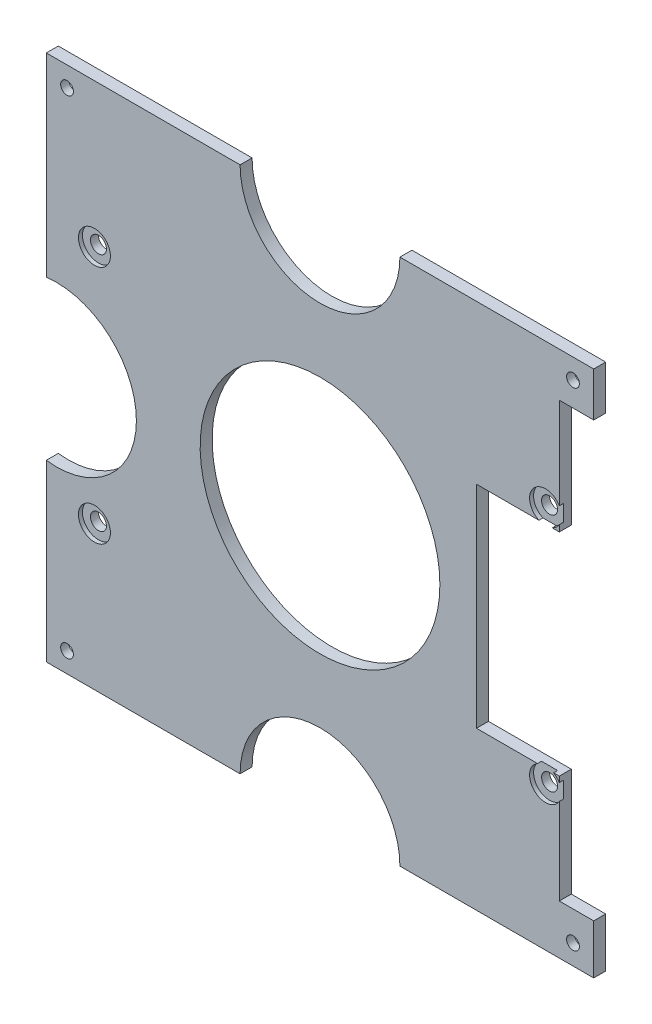
SolidWorks part; units mm, degrees
other "标注1"
sketch "草图4" plane through (-68.5, 66, 6) normal (-0.1703, 0.1692, 0.9708) x (-0.9826, 0.0447, -0.1801)
ref_plane "前视基准面" through (0, 0, 0) normal (0, 0, 1) x (1, 0, 0)
ref_plane "上视基准面" through (0, 0, 0) normal (0, 1, 0) x (1, 0, 0)
ref_plane "右视基准面" through (0, 0, 0) normal (1, 0, 0) x (0, 0, -1)
sketch "草图1" plane through (0, 0, 0) normal (0, 0, 1) x (1, 0, 0)
  line L0 (0, -55) -> (0, 55) construction
  line L1 (-68.5, 66) -> (68.5, 66)
  line L2 (-68.5, 66) -> (-68.5, -66)
  line L3 (-68.5, -66) -> (68.5, -66)
  line L4 (68.5, 66) -> (68.5, -66)
  line L5 (-68.5, 66) -> (68.5, -66) construction
  line L6 (-68.5, -66) -> (68.5, 66) construction
  line L7 (55, 0) -> (-55, 0) construction
  circle A0 centre (63.3106, -61) radius 1.6
  circle A1 centre (-63.3106, -61) radius 1.6
  circle A2 centre (-63.3106, 61) radius 1.6
  circle A3 centre (63.3106, 61) radius 1.6
  circle A4 centre (0, 66) radius 20
  circle A5 centre (0, -66) radius 20
  circle A6 centre (-65.9544, -2.4527) radius 20
  circle A7 centre (65.9544, 2.4527) radius 20
  point P0 (0, 0)
  dimension "D3" = 3.2
  dimension "D4" = 5
  dimension "D5" = 5.1894
  dimension "D6" = 40
  dimension "D1" = 137
  dimension "D2" = 132
extrude "凸台-拉伸1" add sketch "草图1" along normal blind 6 contours A7 L4 L1 A4 L2 A6 L3 A5 A1 A0 A2 A3
sketch "草图2" plane through (0, 0, 6) normal (0, 0, 1) x (1, 0, 0)
  circle A0 centre (0, 0) radius 30
  dimension "D1" = 60
extrude "切除-拉伸1" cut sketch "草图2" against normal blind 13
sketch "草图3" plane through (0, 0, 0) normal (0, 0, -1) x (-1, 0, 0)
  line L0 (0, 2.2) -> (0, -2.2) construction
  line L1 (2.2, 0) -> (-2.2, 0) construction
  circle A0 centre (-63.3106, 61) radius 3.5
  circle A1 centre (63.3106, 61) radius 3.5
  circle A2 centre (-63.3106, -61) radius 3.5
  circle A3 centre (63.3106, -61) radius 3.5
  dimension "D1" = 7
extrude "切除-拉伸2" cut sketch "草图3" against normal blind 3
sketch "草图5" plane through (0, 0, 6) normal (0, 0, 1) x (1, 0, 0)
  line L0 (0, -3.3) -> (0, 3.3) construction
  line L1 (3.3, 0) -> (-3.3, 0) construction
  circle A0 centre (56.45, 30) radius 2
  circle A1 centre (-56.45, 30) radius 2
  circle A2 centre (-56.45, -30) radius 2
  circle A3 centre (56.45, -30) radius 2
  dimension "D1" = 30
  dimension "D2" = 56.45
  dimension "D3" = 4
extrude "切除-拉伸3" cut sketch "草图5" against normal blind 23.5
sketch "草图6" plane through (0, 0, 6) normal (0, 0, 1) x (1, 0, 0)
  line L0 (3.3, 0) -> (-3.3, 0) construction
  line L1 (0, -3.3) -> (0, 3.3) construction
  circle A0 centre (56.45, 30) radius 4
  circle A1 centre (56.45, -30) radius 4
  circle A2 centre (-56.45, -30) radius 4
  circle A3 centre (-56.45, 30) radius 4
  dimension "D1" = 8
extrude "切除-拉伸4" cut sketch "草图6" against normal blind 2
sketch "草图8" plane through (0, 66, 0) normal (0, 1, 0) x (1, 0, 0)
  line L0 (68.5, -6) -> (68.5, 0) construction
  line L1 (-68.5, 0) -> (68.5, 0)
  line L2 (-68.5, 0) -> (-68.5, -2)
  line L3 (-68.5, -2) -> (68.5, -2)
  line L4 (68.5, 0) -> (68.5, -2)
  dimension "D1" = 2
extrude "切除-拉伸6" cut sketch "草图8" against normal up to next
sketch "草图9" plane through (68.5, 0, 0) normal (1, 0, 0) x (0, 0, -1)
  line L0 (-6, -66) -> (-2, -66) construction
  line L1 (-6, 66) -> (-5, 66)
  line L2 (-6, 66) -> (-6, -66)
  line L3 (-6, -66) -> (-5, -66)
  line L4 (-5, 66) -> (-5, -66)
  dimension "D1" = 1
extrude "切除-拉伸7" cut sketch "草图9" against normal up to next
sketch "草图10" plane through (0, 0, 5) normal (0, 0, 1) x (1, 0, 0)
  line L0 (68.5, -66) -> (68.5, -17.3847) construction
  line L1 (68.5, -26.5418) -> (39.163, -26.5418)
  line L2 (68.5, -26.5418) -> (68.5, 26.357)
  line L3 (68.5, 26.357) -> (39.163, 26.357)
  line L4 (39.163, -26.5418) -> (39.163, 26.357)
  line L5 (68.5, 22.29) -> (68.5, 66) construction
  point P6 (68.5, 26.357)
  point P9 (0, 0)
  point P10 (68.5, -26.5418)
extrude "切除-拉伸11" cut sketch "草图10" against normal blind 10
sketch "草图11" plane through (0, 0, 5) normal (0, 0, 1) x (1, 0, 0)
  line L0 (68.5, -66) -> (68.5, -26.5418) construction
  line L1 (68.5, -53.6197) -> (59.8906, -53.6197)
  line L2 (68.5, -53.6197) -> (68.5, 54.9304)
  line L3 (68.5, 54.9304) -> (59.8906, 54.9304)
  line L4 (59.8906, -53.6197) -> (59.8906, 54.9304)
extrude "切除-拉伸12" cut sketch "草图11" against normal blind 10
